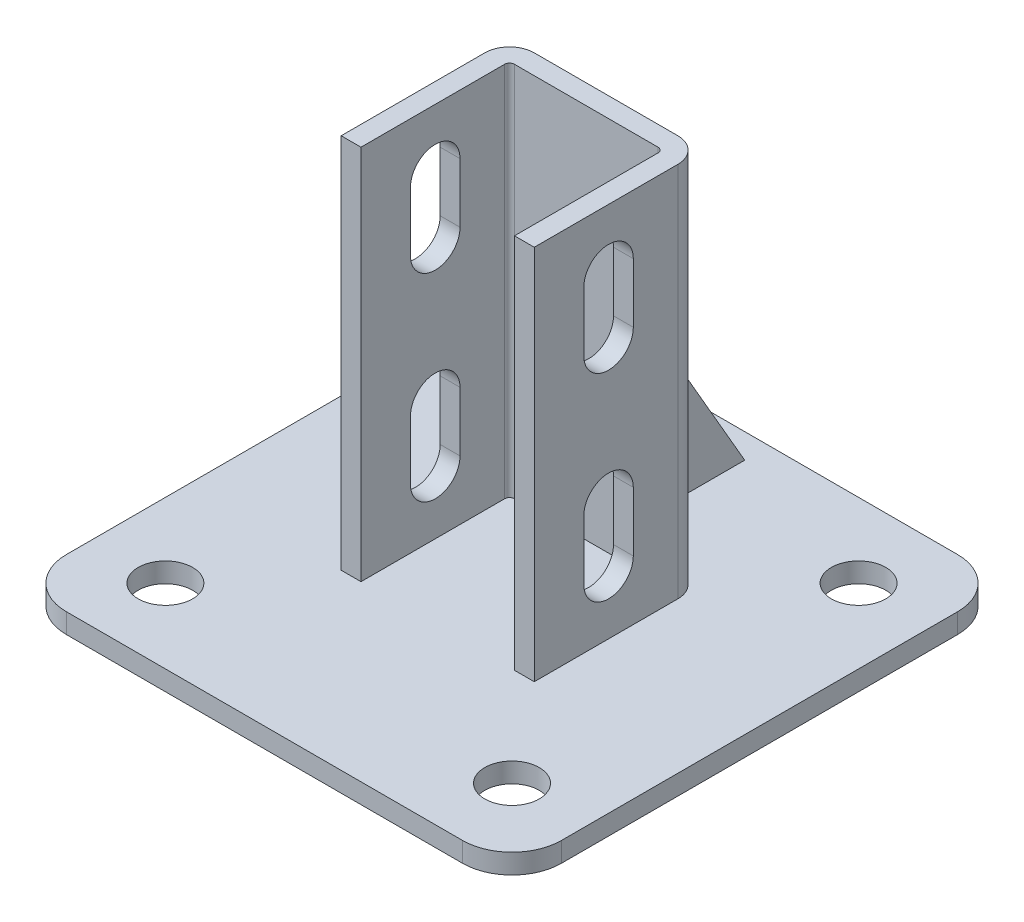
SolidWorks part; units mm, degrees
material "Ст3пс ГОСТ 380-2005"
ref_plane "Спереди" through (0, 0, 0) normal (0, 0, 1) x (1, 0, 0)
ref_plane "Сверху" through (0, 0, 0) normal (0, 1, 0) x (1, 0, 0)
ref_plane "Справа" through (0, 0, 0) normal (1, 0, 0) x (0, 0, -1)
sketch "Эскиз2" plane through (0, 0, 0) normal (0, 1, 0) x (1, 0, 0)
  line L1 (-50, -50) -> (50, -50)
  line L2 (-50, -50) -> (-50, 50)
  line L3 (-50, 50) -> (50, 50)
  line L4 (50, -50) -> (50, 50)
  line L5 (-50, -50) -> (50, 50) construction
  line L6 (-50, 50) -> (50, -50) construction
  point P0 (0, 0)
  dimension "D1" = 100
extrude "Бобышка-Вытянуть1" add sketch "Эскиз2" along normal blind 4
sketch "Эскиз3" plane through (0, 4, 0) normal (0, 1, 0) x (1, 0, 0)
  line L0 (-15.5, -15) -> (-15.5, 15)
  line L1 (-15.5, 15) -> (15.5, 15)
  line L2 (15.5, 15) -> (15.5, -15)
  point P2 (0, 15)
  point P5 (-15.5, 0)
  dimension "D2" = 31
  dimension "D3" = 30
extrude "Вытянуть-Тонкостенный1" add sketch "Эскиз3" along normal offset from surface (76 mm away) 80 thin up to face at (0, 0, 0) thin type one direction reverse wall 4
sketch "Эскиз4" plane through (0, 0, 0) normal (1, 0, 0) x (0, 0, -1)
  line L0 (19, 49.0333) -> (45, 4)
  line L1 (19, 80) -> (19, 4) construction
  line L2 (-50, 4) -> (50, 4) construction
  line L3 (45, 4) -> (19, 4)
  line L4 (19, 4) -> (19, 49.0333)
  line L5 (50, 4) -> (50, 0) construction
  dimension "D1" = 30
  dimension "D2" = 5
extrude "Бобышка-Вытянуть2" add sketch "Эскиз4" along normal mid plane 4
sketch "Эскиз5" plane through (19.5, 0, 0) normal (1, 0, 0) x (0, 0, -1)
  line L0 (0, 68) -> (0, 56) construction
  line L1 (5, 68) -> (5, 56)
  line L2 (-5, 68) -> (-5, 56)
  line L3 (0, 28) -> (0, 16) construction
  line L4 (5, 28) -> (5, 16)
  line L5 (-5, 28) -> (-5, 16)
  line L6 (-15, 80) -> (14, 80) construction
  line L7 (-50, 4) -> (50, 4) construction
  arc A0 (5, 68) -> (-5, 68) centre (0, 68) ccw
  arc A1 (-5, 56) -> (5, 56) centre (0, 56) ccw
  arc A2 (5, 28) -> (-5, 28) centre (0, 28) ccw
  arc A3 (-5, 16) -> (5, 16) centre (0, 16) ccw
  point P3 (0, 62)
  point P8 (0, 22)
  dimension "D2" = 12
  dimension "D4" = 12
  dimension "D1" = 10
  dimension "D3" = 12
extrude "Вырез-Вытянуть1" cut sketch "Эскиз5" against normal through all
sketch "Эскиз6" plane through (0, 4, 0) normal (0, 1, 0) x (1, 0, 0)
  line L0 (-50, 50) -> (-50, -50) construction
  line L1 (35, -35) -> (-35, -35) construction
  line L2 (35, -35) -> (35, 35) construction
  line L3 (35, 35) -> (-35, 35) construction
  line L4 (-35, -35) -> (-35, 35) construction
  line L5 (35, -35) -> (-35, 35) construction
  line L6 (35, 35) -> (-35, -35) construction
  line L7 (50, 50) -> (-50, 50) construction
  circle A0 centre (-35, 35) radius 5.5
  circle A1 centre (-35, -35) radius 5.5
  circle A2 centre (35, 35) radius 5.5
  circle A3 centre (35, -35) radius 5.5
  point P0 (0, 0)
  dimension "D1" = 11
  dimension "D2" = 15
  dimension "D3" = 15
extrude "Вырез-Вытянуть2" cut sketch "Эскиз6" against normal through all
fillet "Скругление1" radius 10 4 edges at (50, 2, 50) (-50, 2, 50) (-50, 2, -50) (50, 2, -50)
